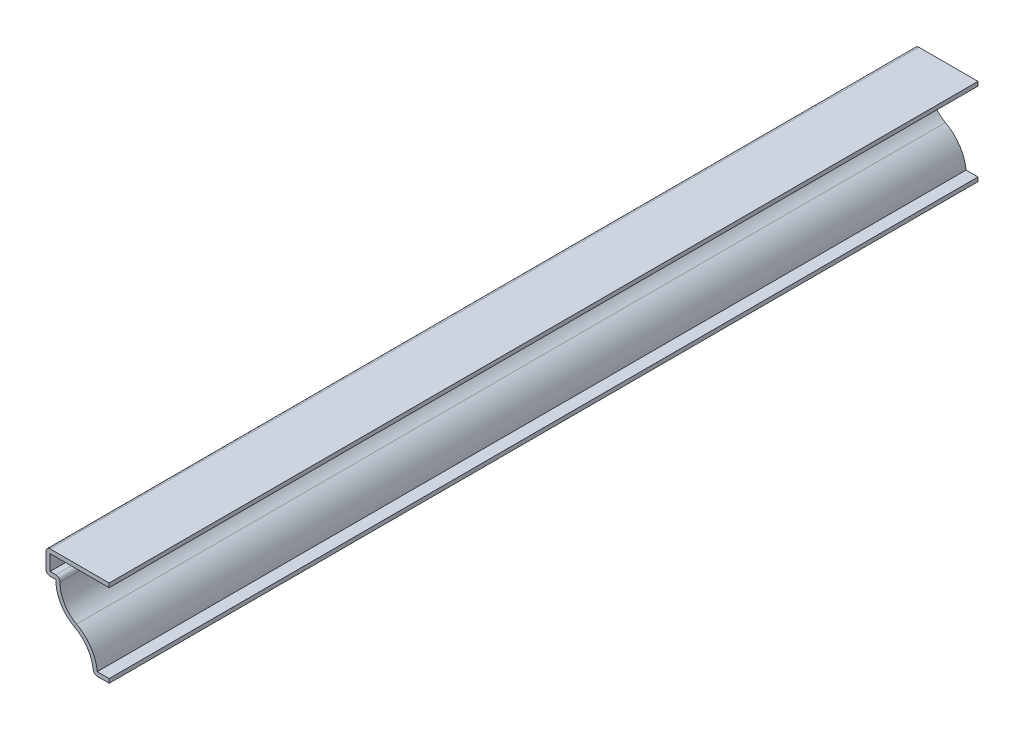
SolidWorks part; units mm, degrees
ref_plane "Front Plane" through (0, 0, 0) normal (0, 0, 1) x (1, 0, 0)
ref_plane "Top Plane" through (0, 0, 0) normal (0, 1, 0) x (1, 0, 0)
ref_plane "Right Plane" through (0, 0, 0) normal (1, 0, 0) x (0, 0, -1)
sketch "Sketch1" plane through (0, 0, 0) normal (0, 0, 1) x (1, 0, 0)
  line L0 (0, 0) -> (0, 34.925) construction
  line L1 (0, 34.925) -> (-25.4, 34.925)
  line L2 (-25.4, 34.925) -> (-25.4, 25.4)
  line L3 (-25.4, 25.4) -> (-21.4313, 25.4)
  line L4 (0, 0) -> (-6.35, 0)
  line L5 (-21.4313, 25.4) -> (-21.4312, 13.1652) construction
  arc A0 (-6.35, 0) -> (-13.8914, 12.5946) centre (-20.6375, 0) ccw
  arc A1 (-13.8914, 12.5946) -> (-21.4313, 25.4) centre (-7.1453, 25.1891) cw
  dimension "D5" = 14.2875
  dimension "D6" = 14.2875
  dimension "D7" = 3.9688
  dimension "D1" = 6.35
  dimension "D2" = 9.525
  dimension "D3" = 15.0812
  dimension "D4" = 34.925
extrude "Extrude-Thin1" add sketch "Sketch1" against normal blind 349.25 thin thin type one direction reverse wall 1.651
fillet "Fillet1" radius 1.651 4 edges at (-6.35, 0, -174.625) (-19.6439, 27.051, -174.625) (-25.4, 25.4, -174.625) (-25.4, 34.925, -174.625)
